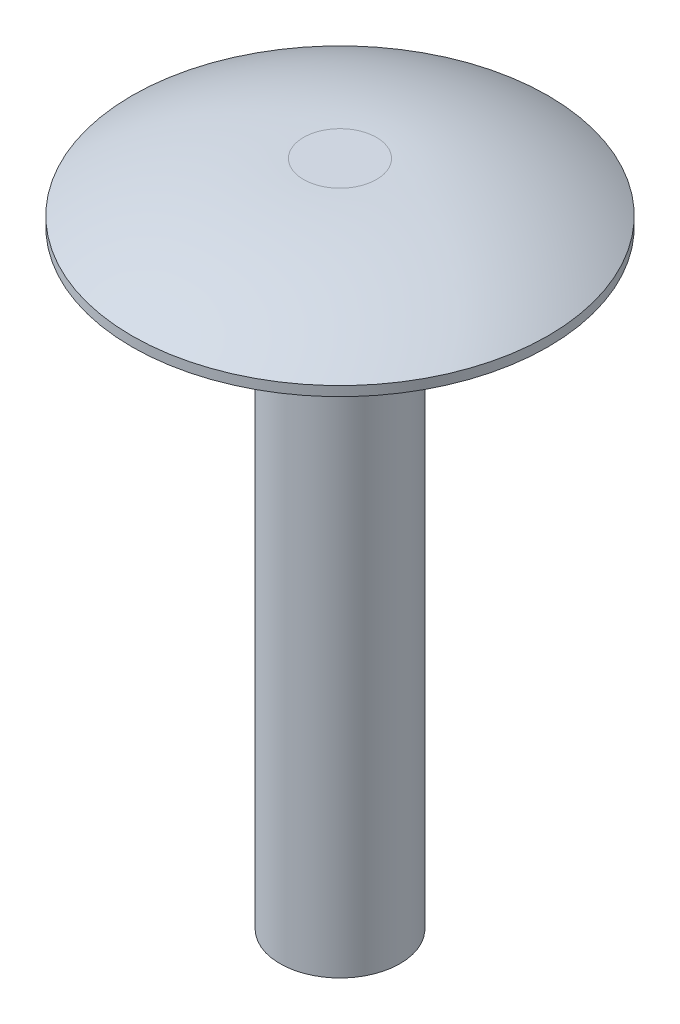
SolidWorks part; units mm, degrees
material "6061 Alloy"
ref_plane "Front Plane" through (0, 0, 0) normal (0, 0, 1) x (1, 0, 0)
ref_plane "Top Plane" through (0, 0, 0) normal (0, 1, 0) x (1, 0, 0)
ref_plane "Right Plane" through (0, 0, 0) normal (1, 0, 0) x (0, 0, -1)
sketch "Sketch1" plane through (0, 0, 0) normal (0, 0, 1) x (1, 0, 0)
  line L5 (-1.4478, 26.4795) -> (0, 26.4795)
  line L6 (0, 0) -> (-2.3813, 0)
  line L7 (0, 0) -> (0, 26.4795)
  line L9 (-2.3813, 0) -> (-2.3813, 24.13)
  line L10 (-2.3813, 24.13) -> (-8.255, 24.13)
  line L12 (0, 26.4795) -> (-8.255, 26.4795) construction
  line L13 (-8.255, 24.13) -> (-8.255, 26.4795) construction
  line L14 (-8.255, 24.511) -> (-8.255, 24.13)
  arc A1 (-8.255, 24.511) -> (-1.4478, 26.4795) centre (-1.4478, 13.7254) cw
  dimension "D1" = 24.13
  dimension "D2" = 2.3813
  dimension "D3" = 8.255
  dimension "D4" = 2.3495
  dimension "D5" = 0.381
  dimension "D6" = 1.4478
revolve "Revolve1" add sketch "Sketch1" angle 360 about L7
